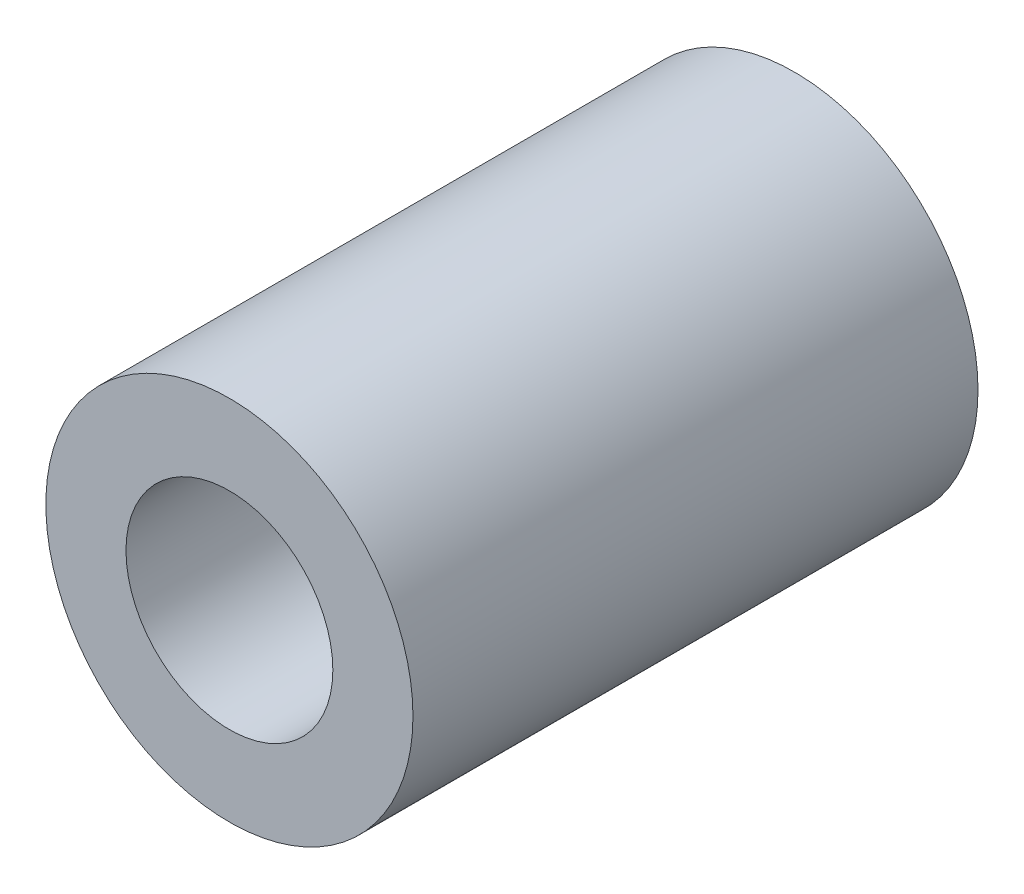
SolidWorks part; units mm, degrees
ref_plane "Front Plane" through (0, 0, 0) normal (0, 0, 1) x (1, 0, 0)
ref_plane "Top Plane" through (0, 0, 0) normal (0, 1, 0) x (1, 0, 0)
ref_plane "Right Plane" through (0, 0, 0) normal (1, 0, 0) x (0, 0, -1)
sketch "Sketch1" plane through (0, 0, 0) normal (0, 0, 1) x (1, 0, 0)
  circle A0 centre (0, 0) radius 3.35
  circle A1 centre (0, 0) radius 5.945
  dimension "D1" = 6.7
  dimension "D2" = 11.89
extrude "Boss-Extrude1" add sketch "Sketch1" along normal blind 18.3
